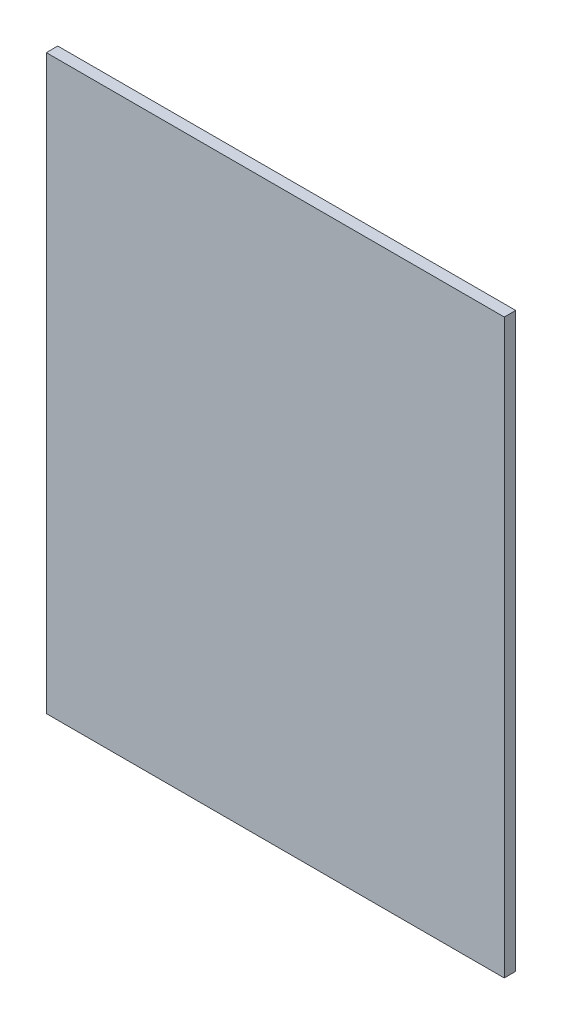
SolidWorks part; units mm, degrees
material "普通碳钢"
ref_plane "Front" through (0, 0, 0) normal (0, 0, 1) x (1, 0, 0)
ref_plane "Top" through (0, 0, 0) normal (0, 1, 0) x (1, 0, 0)
ref_plane "Right" through (0, 0, 0) normal (1, 0, 0) x (0, 0, -1)
sketch "草图1" plane through (0, 0, 0) normal (0, 0, 1) x (1, 0, 0)
  line L1 (0, 0) -> (800, 0)
  line L2 (0, 0) -> (0, 1000)
  line L3 (0, 1000) -> (800, 1000)
  line L4 (800, 0) -> (800, 1000)
  dimension "D1" = 800
  dimension "D2" = 1000
extrude "凸台-拉伸1" add sketch "草图1" along normal blind 20
shell "抽壳1" thickness 1.8
